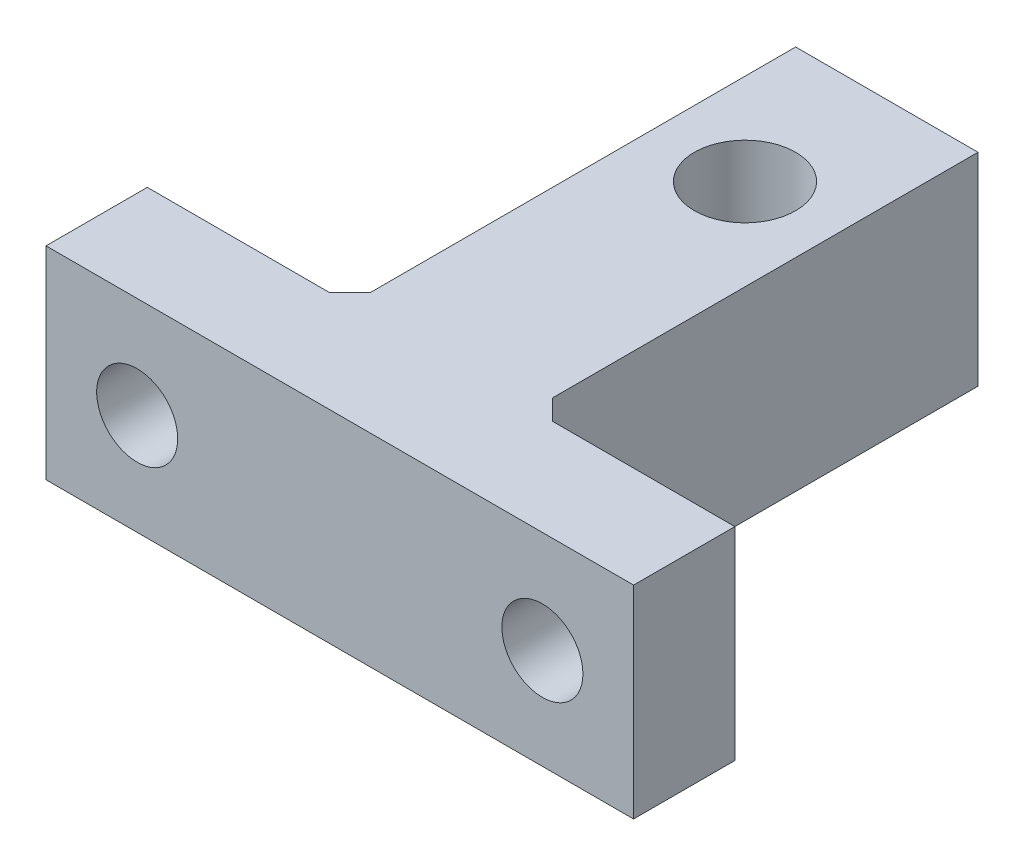
SolidWorks part; units mm, degrees
ref_plane "Front Plane" through (0, 0, 0) normal (0, 0, 1) x (1, 0, 0)
ref_plane "Top Plane" through (0, 0, 0) normal (0, 1, 0) x (1, 0, 0)
ref_plane "Right Plane" through (0, 0, 0) normal (1, 0, 0) x (0, 0, -1)
sketch "Sketch1" plane through (0, 0, 0) normal (0, 1, 0) x (1, 0, 0)
  line L0 (-1.5776, 0) -> (-16.0776, 0)
  line L1 (-16.0776, 0) -> (-16.0776, 5)
  line L2 (-16.0776, 5) -> (-6.0776, 5)
  line L3 (-6.0776, 5) -> (-6.0776, 27)
  line L4 (-6.0776, 27) -> (2.9224, 27)
  line L5 (2.9224, 27) -> (2.9224, 5)
  line L6 (2.9224, 5) -> (12.9224, 5)
  line L7 (12.9224, 5) -> (12.9224, 0)
  line L8 (12.9224, 0) -> (-1.5776, 0)
  line L9 (-1.5776, 0) -> (-1.5776, 20) construction
  circle A0 centre (-1.5776, 20) radius 2.5
  point P12 (0, 0)
  dimension "D1" = 29
  dimension "D2" = 5
  dimension "D3" = 22
  dimension "D4" = 9
  dimension "D5" = 10
extrude "Boss-Extrude1" add sketch "Sketch1" along normal blind 10
sketch "Sketch2" plane through (0, 0, 0) normal (0, 0, 1) x (1, 0, 0)
  line L3 (-16.0776, 10) -> (-1.5776, 10)
  line L5 (-1.5776, 10) -> (-1.5776, 5)
  circle A0 centre (-11.5776, 5) radius 2
  circle A1 centre (8.4224, 4.9503) radius 2
  point P4 (0, 0)
  dimension "D1" = 20
  dimension "D3" = 4
  dimension "D4" = 4
  dimension "D2" = 5
  dimension "D5" = 14.5
  dimension "D6" = 10
extrude "Cut-Extrude1" cut sketch "Sketch2" against normal blind 10 contours A0 | A1
sketch "Sketch3" plane through (0, 0, -27) normal (0, 0, -1) x (-1, 0, 0)
  line L0 (-2.9224, 0) -> (6.0776, 0) construction
  line L1 (-2.9224, 10) -> (-2.9224, 0) construction
  circle A0 centre (1.5776, 5) radius 1.5
  dimension "D1" = 5
  dimension "D2" = 4.5
extrude "Cut-Extrude2" cut sketch "Sketch3" against normal blind 4
cosmetic thread "Cosmetic Thread1" parameters "D1"=5, "D2"=4
chamfer "Chamfer1" distance 1 angle 45 2 edges at (-6.0776, 5, -5) (2.9224, 5, -5)
